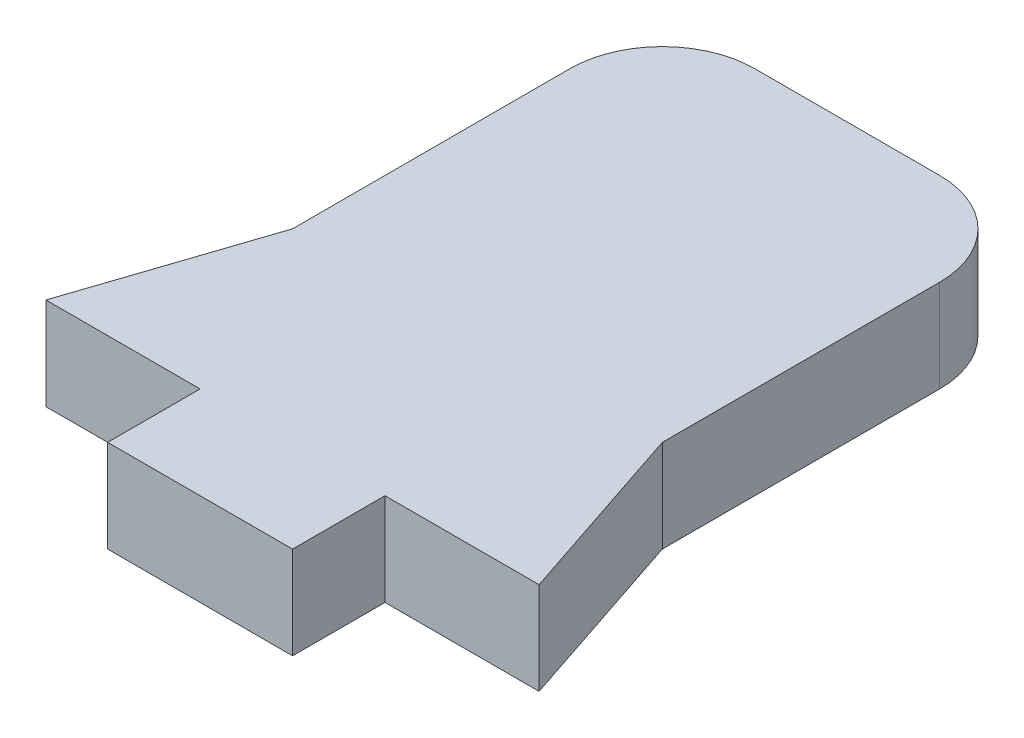
SolidWorks part; units mm, degrees
material "Acrylic (Medium-high impact)"
ref_plane "Plano frontal" through (0, 0, 0) normal (0, 0, 1) x (1, 0, 0)
ref_plane "Plano superior" through (0, 0, 0) normal (0, 1, 0) x (1, 0, 0)
ref_plane "Plano direito" through (0, 0, 0) normal (1, 0, 0) x (0, 0, -1)
sketch "Sketch6" plane through (0, 0, 0) normal (0, 1, 0) x (1, 0, 0)
  line L1 (-3, 10.5) -> (3, 10.5)
  line L2 (-6, 7.5) -> (-6, -7.5)
  line L3 (-6, -7.5) -> (6, -7.5)
  line L4 (6, 7.5) -> (6, -7.5)
  arc A0 (3, 10.5) -> (6, 7.5) centre (3, 7.5) cw
  arc A1 (-3, 10.5) -> (-6, 7.5) centre (-3, 7.5) ccw
  point P4 (0, 10.5)
  point P6 (-6, 0)
  point P9 (6, 10.5)
  point P12 (-6, 10.5)
  dimension "D3" = 3
  dimension "D1" = 12
  dimension "D2" = 18
extrude "Boss-Extrude4" add sketch "Sketch6" along normal mid plane 3
sketch "Sketch8" plane through (0, 0, 0) normal (0, 1, 0) x (1, 0, 0)
  line L5 (-6, -7.5) -> (6, -7.5) construction
  line L6 (-3, -7.5) -> (3, -7.5)
  line L7 (-3, -7.5) -> (-3, -10.5)
  line L8 (-3, -10.5) -> (3, -10.5)
  line L9 (3, -7.5) -> (3, -10.5)
  point P14 (0, -7.5)
  dimension "D1" = 3
  dimension "D3" = 6
extrude "Boss-Extrude5" add sketch "Sketch8" along normal mid plane 3
sketch "Sketch9" plane through (0, 0, 0) normal (0, 1, 0) x (1, 0, 0)
  line L0 (-6, -1.5) -> (-8, -7.5)
  line L1 (-6, 7.5) -> (-6, -7.5) construction
  line L2 (-8, -7.5) -> (-6, -7.5)
  line L3 (-6, -1.5) -> (-6, -7.5)
  line L4 (0, -1.65) -> (0, 1.65) construction
  line L5 (6, -1.5) -> (6, -7.5)
  line L6 (8, -7.5) -> (6, -7.5)
  line L7 (6, -1.5) -> (8, -7.5)
  dimension "D1" = 2
  dimension "D2" = 6
extrude "Boss-Extrude6" add sketch "Sketch9" along normal mid plane 3
